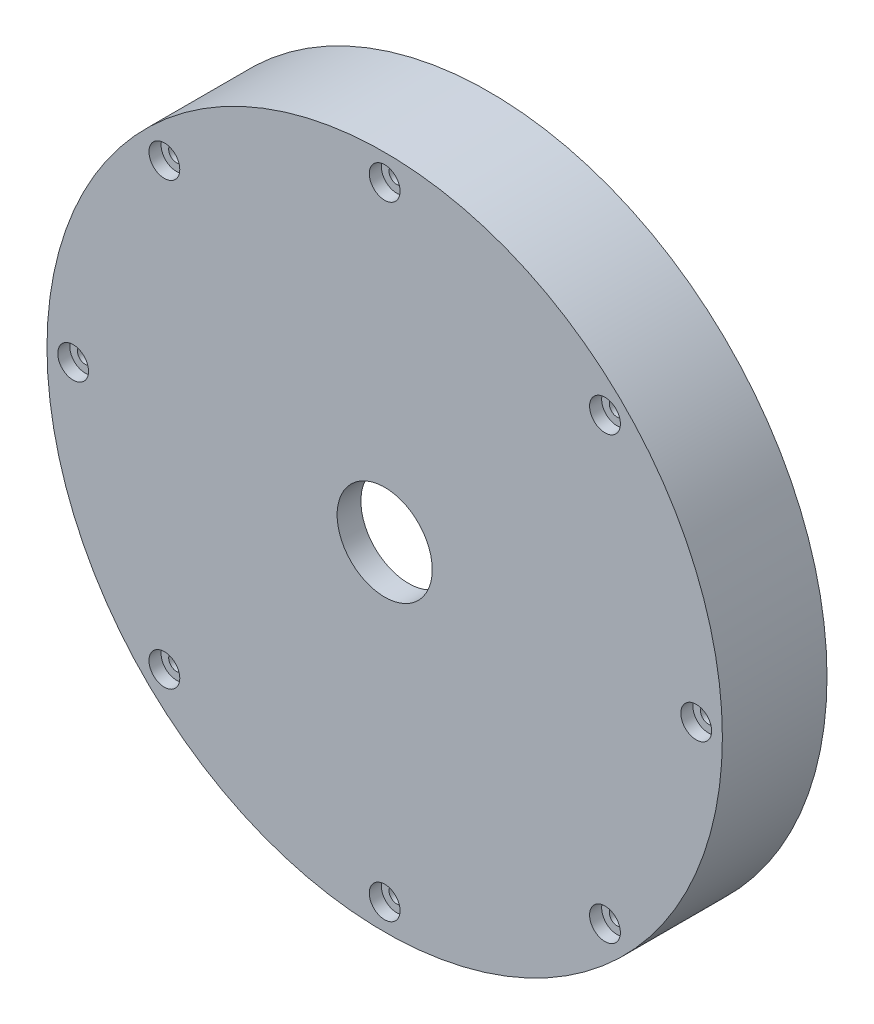
SolidWorks part; units mm, degrees
ref_plane "Front Plane" through (0, 0, 0) normal (0, 0, 1) x (1, 0, 0)
ref_plane "Top Plane" through (0, 0, 0) normal (0, 1, 0) x (1, 0, 0)
ref_plane "Right Plane" through (0, 0, 0) normal (1, 0, 0) x (0, 0, -1)
sketch "Sketch1" plane through (0, 0, 0) normal (0, 0, 1) x (1, 0, 0)
  circle A0 centre (0, 0) radius 60
  circle A1 centre (0, 0) radius 71
  dimension "D1" = 120
  dimension "D2" = 142
extrude "Boss-Extrude1" add sketch "Sketch1" along normal blind 17
sketch "Sketch2" plane through (0, 0, 17) normal (0, 0, 1) x (1, 0, 0)
  circle A0 centre (0, 0) radius 71
  circle A1 centre (0, 0) radius 10
  dimension "D1" = 20
extrude "Boss-Extrude2" add sketch "Sketch2" along normal blind 5
sketch "Sketch5" plane through (0, 0, 22) normal (0, 0, 1) x (1, 0, 0)
  line L3 (0, 0) -> (0, 65.5) construction
  circle A11 centre (0, 65.5) radius 1.637
  circle A12 centre (46.3155, 46.3155) radius 1.637
  circle A13 centre (65.5, 0) radius 1.637
  circle A14 centre (46.3155, -46.3155) radius 1.637
  circle A15 centre (0, -65.5) radius 1.637
  circle A16 centre (-46.3155, -46.3155) radius 1.637
  circle A17 centre (-65.5, 0) radius 1.637
  circle A18 centre (-46.3155, 46.3155) radius 1.637
  point P17 (0, 0)
  dimension "D4" = 3.2741
  dimension "D1" = 8
  dimension "D2" = 65.5
extrude "Cut-Extrude1" cut sketch "Sketch5" against normal through all
sketch "Sketch6" plane through (0, 0, 22) normal (0, 0, 1) x (1, 0, 0)
  circle A0 centre (0, 65.5) radius 3.2385
  circle A1 centre (46.3155, 46.3155) radius 3.2385
  circle A2 centre (65.5, 0) radius 3.2385
  circle A3 centre (46.3155, -46.3155) radius 3.2385
  circle A4 centre (0, -65.5) radius 3.2385
  circle A5 centre (-46.3155, -46.3155) radius 3.2385
  circle A6 centre (-65.5, 0) radius 3.2385
  circle A7 centre (-46.3155, 46.3155) radius 3.2385
  point P20 (0, 0)
  dimension "D1" = 6.477
  dimension "D2" = 8
extrude "Cut-Extrude2" cut sketch "Sketch6" against normal blind 2.54
